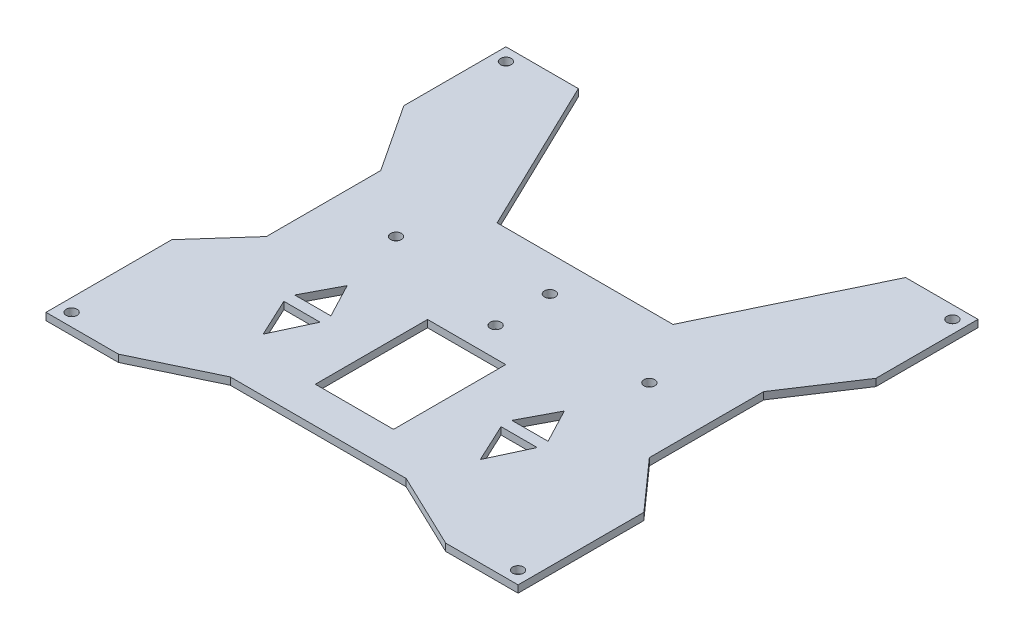
SolidWorks part; units mm, degrees
ref_plane "Front Plane" through (0, 0, 0) normal (0, 0, 1) x (1, 0, 0)
ref_plane "Top Plane" through (0, 0, 0) normal (0, 1, 0) x (1, 0, 0)
ref_plane "Right Plane" through (0, 0, 0) normal (1, 0, 0) x (0, 0, -1)
sketch "Sketch1" plane through (0, 0, 0) normal (0, 1, 0) x (1, 0, 0)
  line L0 (0, 0) -> (123.36, 0) construction
  line L1 (123.36, 0) -> (123.36, -120) construction
  line L2 (0, 0) -> (0, -120) construction
  line L3 (0, 0) -> (-3.5355, 3.5355) construction
  line L4 (123.36, -120) -> (126.8955, -123.5355) construction
  line L6 (-3.5355, 3.5355) -> (126.8955, 3.5355)
  line L7 (-3.5355, 3.5355) -> (-3.5355, -123.5355)
  line L8 (-3.5355, -123.5355) -> (126.8955, -123.5355)
  line L9 (126.8955, 3.5355) -> (126.8955, -123.5355)
  circle A0 centre (0, 0) radius 1.5
  circle A1 centre (123.36, 0) radius 1.5
  circle A2 centre (123.36, -120) radius 1.5
  circle A3 centre (0, -120) radius 1.5
  dimension "D1" = 123.36
  dimension "D2" = 120
  dimension "D3" = 5
  dimension "D4" = 5
extrude "Boss-Extrude1" add sketch "Sketch1" along normal blind 2 contours L9 L6 L7 L8 A3 A2 A1 A0
sketch "Sketch3" plane through (0, 2, 0) normal (0, 1, 0) x (1, 0, 0)
  line L0 (-3.5355, -60) -> (126.8955, -60) construction
  line L5 (-3.5355, 3.5355) -> (-3.5355, -123.5355) construction
  line L6 (126.8955, 3.5355) -> (126.8955, -123.5355) construction
  line L7 (-3.5355, 3.5355) -> (16.4645, 3.5355) construction
  line L8 (-3.5355, 3.5355) -> (126.8955, 3.5355) construction
  line L10 (61.68, -60) -> (61.68, -45.9381) construction
  line L13 (16.4645, 3.5355) -> (106.8955, 3.5355)
  line L14 (-3.5355, -39.8122) -> (126.8955, -39.8122) construction
  line L15 (16.4645, 3.5355) -> (37.3799, -39.8122)
  line L16 (61.68, -45.9381) -> (61.68, -28.036) construction
  line L17 (37.3799, -39.8122) -> (85.9801, -39.8122)
  line L18 (106.8955, 3.5355) -> (85.9801, -39.8122)
  point P20 (61.68, -39.8122)
  dimension "D1" = 20
extrude "Cut-Extrude2" cut sketch "Sketch3" against normal blind 2
sketch "Sketch4" plane through (0, 2, 0) normal (0, 1, 0) x (1, 0, 0)
  line L0 (61.68, -123.5355) -> (61.68, -113.5355) construction
  line L1 (-3.5355, -123.5355) -> (126.8955, -123.5355) construction
  line L2 (-3.5355, -123.5355) -> (16.4645, -123.5355) construction
  line L3 (37.3799, -39.8122) -> (37.3799, -113.5355) construction
  line L4 (85.9801, -113.5355) -> (37.3799, -113.5355)
  line L5 (37.3799, -113.5355) -> (16.4645, -123.5355)
  line L6 (85.9801, -113.5355) -> (106.8955, -123.5355)
  line L7 (16.4645, -123.5355) -> (106.8955, -123.5355)
  dimension "D1" = 10
  dimension "D2" = 20
extrude "Cut-Extrude3" cut sketch "Sketch4" against normal blind 2
sketch "Sketch5" plane through (0, 2, 0) normal (0, 1, 0) x (1, 0, 0)
  line L0 (61.68, -113.5355) -> (61.68, -103.5355) construction
  line L1 (85.9801, -113.5355) -> (37.3799, -113.5355) construction
  line L2 (61.68, -103.5355) -> (61.68, -72.5355) construction
  line L3 (72.48, -88.0355) -> (50.88, -88.0355) construction
  line L4 (50.88, -88.0355) -> (50.88, -72.5355) construction
  line L5 (72.48, -88.0355) -> (72.48, -103.5355) construction
  line L7 (50.88, -72.5355) -> (72.48, -72.5355)
  line L8 (50.88, -72.5355) -> (50.88, -103.5355)
  line L9 (50.88, -103.5355) -> (72.48, -103.5355)
  line L10 (72.48, -72.5355) -> (72.48, -103.5355)
  point P8 (61.68, -88.0355)
  dimension "D1" = 10
  dimension "D2" = 31
  dimension "D3" = 10.8
extrude "Cut-Extrude4" cut sketch "Sketch5" against normal blind 10
sketch "Sketch6" plane through (0, 2, 0) normal (0, 1, 0) x (1, 0, 0)
  line L0 (61.68, -72.5355) -> (61.68, -64.5355) construction
  line L1 (72.48, -72.5355) -> (50.88, -72.5355) construction
  line L2 (61.68, -64.5355) -> (61.68, -49.5355) construction
  line L3 (61.68, -57.0355) -> (26.68, -57.0355) construction
  circle A0 centre (61.68, -64.5355) radius 1.5
  circle A1 centre (61.68, -49.5355) radius 1.5
  circle A2 centre (26.68, -57.0355) radius 1.5
  circle A3 centre (96.68, -57.0355) radius 1.5
  dimension "D2" = 15
  dimension "D3" = 35
  dimension "D1" = 8
extrude "Cut-Extrude5" cut sketch "Sketch6" against normal blind 10
sketch "Sketch7" plane through (0, 2, 0) normal (0, 1, 0) x (1, 0, 0)
  line L0 (61.68, -103.5355) -> (61.68, -72.5355) construction
  line L1 (50.88, -103.5355) -> (72.48, -103.5355) construction
  line L2 (72.48, -72.5355) -> (50.88, -72.5355) construction
  line L3 (61.68, -72.5355) -> (61.68, -88.0355) construction
  line L4 (61.68, -88.0355) -> (31.68, -88.0355) construction
  line L5 (31.68, -88.0355) -> (31.68, -85.0355) construction
  line L6 (36.68, -85.0355) -> (26.68, -85.0355)
  line L7 (26.68, -85.0355) -> (31.68, -75.5375)
  line L8 (36.68, -85.0355) -> (31.68, -75.5375)
  line L9 (31.68, -88.0355) -> (26.68, -88.0355)
  line L10 (26.68, -88.0355) -> (31.68, -98.7582)
  line L11 (31.68, -98.7582) -> (36.68, -88.0355)
  line L12 (36.68, -88.0355) -> (31.68, -88.0355)
  line L13 (86.68, -85.0355) -> (91.68, -75.5375)
  line L14 (96.68, -85.0355) -> (91.68, -75.5375)
  line L15 (86.68, -85.0355) -> (96.68, -85.0355)
  line L16 (91.68, -98.7582) -> (86.68, -88.0355)
  line L17 (96.68, -88.0355) -> (91.68, -98.7582)
  line L18 (91.68, -88.0355) -> (96.68, -88.0355)
  line L19 (86.68, -88.0355) -> (91.68, -88.0355)
  dimension "D1" = 30
  dimension "D2" = 3
  dimension "D3" = 5
extrude "Cut-Extrude6" cut sketch "Sketch7" against normal blind 10 contours L11 L12 L9 L10 | L6 L8 L7 | L19 L16 L17 L18 | L13 L15 L14
sketch "Sketch8" plane through (0, 2, 0) normal (0, 1, 0) x (1, 0, 0)
  line L0 (-3.5355, 3.5355) -> (-3.5355, -123.5355) construction
  line L1 (-3.5355, -60) -> (8.7805, -60) construction
  line L2 (8.7805, -60) -> (8.7805, -43.3637)
  line L3 (8.7805, -43.3637) -> (-3.5355, -24.6713)
  line L4 (8.7805, -60) -> (8.7805, -74.9539)
  line L5 (8.7805, -74.9539) -> (-3.5355, -88.7863)
  line L6 (-3.5355, -24.6713) -> (-3.5355, -88.7863)
  line L7 (61.68, -113.5355) -> (61.68, -108.6003) construction
  line L8 (85.9801, -113.5355) -> (37.3799, -113.5355) construction
  line L9 (114.5795, -43.3637) -> (126.8955, -24.6713)
  line L10 (114.5795, -60) -> (114.5795, -43.3637)
  line L11 (114.5795, -60) -> (114.5795, -74.9539)
  line L12 (114.5795, -74.9539) -> (126.8955, -88.7863)
  line L13 (126.8955, -24.6713) -> (126.8955, -88.7863)
extrude "Cut-Extrude7" cut sketch "Sketch8" against normal blind 10 contours L6 L5 L4 L2 L3 | L9 L13 L12 L11 L10
sketch "Sketch9" plane through (0, 2, 0) normal (0, 1, 0) x (1, 0, 0)
  line L0 (61.68, -49.5355) -> (61.68, -64.5355) construction
